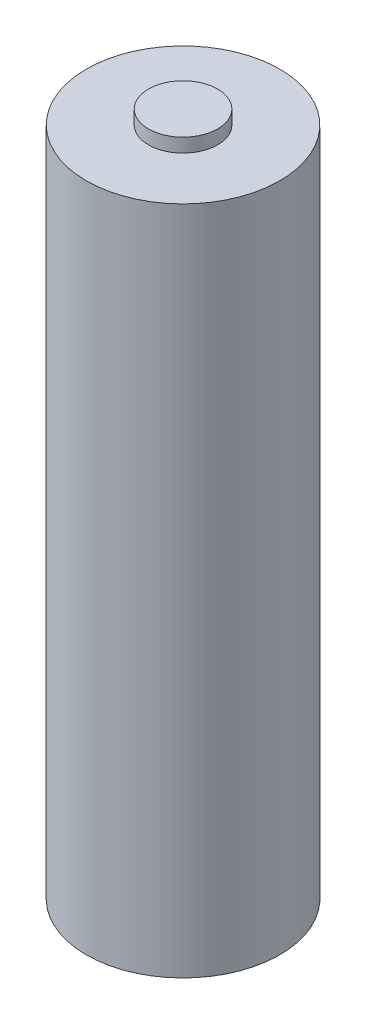
SolidWorks part; units mm, degrees
ref_plane "Front Plane" through (0, 0, 0) normal (0, 0, 1) x (1, 0, 0)
ref_plane "Top Plane" through (0, 0, 0) normal (0, 1, 0) x (1, 0, 0)
ref_plane "Right Plane" through (0, 0, 0) normal (1, 0, 0) x (0, 0, -1)
sketch "Sketch1" plane through (0, 0, 0) normal (0, 1, 0) x (1, 0, 0)
  circle A0 centre (0, 0) radius 7
  dimension "D1" = 14
extrude "Boss-Extrude1" add sketch "Sketch1" along normal blind 48.5
sketch "Sketch2" plane through (0, 48.5, 0) normal (0, 1, 0) x (1, 0, 0)
  circle A0 centre (0, 0) radius 2.5
  dimension "D1" = 5
extrude "Boss-Extrude2" add sketch "Sketch2" along normal blind 1
sketch "Sketch3" plane through (0, 0, 0) normal (0, -1, 0) x (-1, 0, 0)
  circle A0 centre (0, 0) radius 3.5
  dimension "D1" = 7
extrude "Cut-Extrude1" cut sketch "Sketch3" against normal blind 0.01
